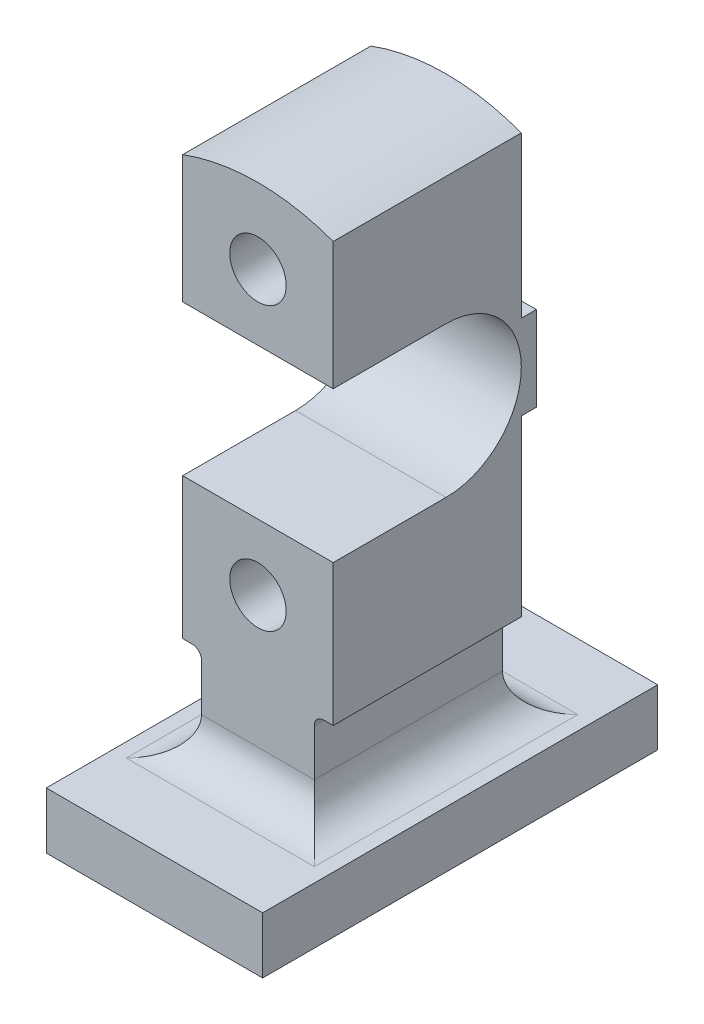
SolidWorks part; units mm, degrees
ref_plane "Front Plane" through (0, 0, 0) normal (0, 0, 1) x (1, 0, 0)
ref_plane "Top Plane" through (0, 0, 0) normal (0, 1, 0) x (1, 0, 0)
ref_plane "Right Plane" through (0, 0, 0) normal (1, 0, 0) x (0, 0, -1)
sketch "Sketch1" plane through (0, 0, 0) normal (1, 0, 0) x (0, 0, -1)
  line L0 (105, -46.1202) -> (105, 424.614) construction
  line L5 (0, 0) -> (210, 0)
  line L6 (0, 0) -> (0, 30)
  line L7 (0, 30) -> (55, 30)
  line L8 (210, 0) -> (210, 30)
  line L9 (55, 310) -> (55, 235)
  line L10 (155, 310) -> (155, 217.5)
  line L11 (163, 217.5) -> (163, 172.5)
  line L12 (163, 217.5) -> (155, 217.5)
  line L13 (163, 172.5) -> (155, 172.5)
  line L14 (155, 172.5) -> (155, 30)
  line L15 (155, 310) -> (55, 310)
  line L16 (55, 235) -> (115, 235)
  line L17 (55, 155) -> (115, 155)
  line L18 (55, 155) -> (55, 30)
  line L19 (155, 30) -> (210, 30)
  arc A0 (115, 155) -> (115, 235) centre (115, 195) ccw
  point P14 (163, 195)
  dimension "D4" = 80
  dimension "D1" = 30
  dimension "D2" = 210
  dimension "D3" = 100
  dimension "D5" = 165
  dimension "D6" = 40
  dimension "D7" = 45
  dimension "D8" = 8
  dimension "D9" = 115
extrude "Boss-Extrude1" add sketch "Sketch1" along normal blind 115
sketch "Sketch2" plane through (0, 0, -155) normal (0, 0, -1) x (-1, 0, 0)
  line L0 (-115, 0) -> (0, 0) construction
  line L2 (-97.5, 302.8193) -> (-97.5, 80)
  line L4 (-17.5, 302.8193) -> (-17.5, 80)
  line L6 (-87.5, 75) -> (-87.5, 50)
  line L7 (-27.5, 75) -> (-27.5, 50)
  line L8 (-57.5, -9.2077) -> (-57.5, 134.7763) construction
  line L9 (-97.5, 80) -> (-92.5, 80)
  line L10 (-22.5, 80) -> (-17.5, 80)
  line L11 (-7.5, 30) -> (0, 30)
  line L12 (-107.5, 30) -> (-115, 30)
  line L13 (0, 30) -> (0, 310)
  line L14 (0, 310) -> (-115, 310)
  line L15 (-115, 310) -> (-115, 30)
  arc A1 (-17.5, 302.8193) -> (-97.5, 302.8193) centre (-57.5, 195) ccw
  arc A2 (-27.5, 75) -> (-22.5, 80) centre (-22.5, 75) cw
  arc A3 (-87.5, 75) -> (-92.5, 80) centre (-92.5, 75) ccw
  arc A4 (-7.5, 30) -> (-27.5, 50) centre (-7.5, 50) cw
  arc A5 (-107.5, 30) -> (-87.5, 50) centre (-107.5, 50) ccw
  point P6 (-57.5, 0)
  point P10 (-27.5, 80)
  line M14 (0, 30) -> (0, 172.5)
  line M15 (0, 172.5) -> (-115, 172.5)
  line M16 (-115, 172.5) -> (-115, 30)
  line M17 (-115, 30) -> (0, 30)
  dimension "D2" = 115
  dimension "D6" = 5
  dimension "D7" = 20
  dimension "D1" = 80
  dimension "D3" = 195
  dimension "D4" = 60
  dimension "D5" = 115
  dimension "D8" = 115
extrude "Cut-Extrude4" cut sketch "Sketch2" against normal through all both and the other way through all contours A4 L4 L10 A2 L7 M17 M14 M15 | A1 L14 L15 L2 M15 | A5 L6 A3 L9 L2 M17 M15 M16 | A1 L4 L13 L14 M15
fillet "Fillet1" radius 20 2 edges at (57.5, 30, -155) (57.5, 30, -55)
sketch "Sketch4" plane through (0, 0, -155) normal (0, 0, -1) x (-1, 0, 0)
  line L0 (-7.5, 30) -> (-107.5, 30) construction
  line L1 (-17.5, 217.5) -> (-17.5, 302.8193) construction
  circle A0 centre (-57.5, 120) radius 15
  circle A1 centre (-57.5, 270) radius 15
  point P4 (0, 0)
  dimension "D1" = 150
  dimension "D3" = 30
  dimension "D2" = 90
  dimension "D4" = 40
extrude "Cut-Extrude5" cut sketch "Sketch4" against normal blind 148 and the other way through all
